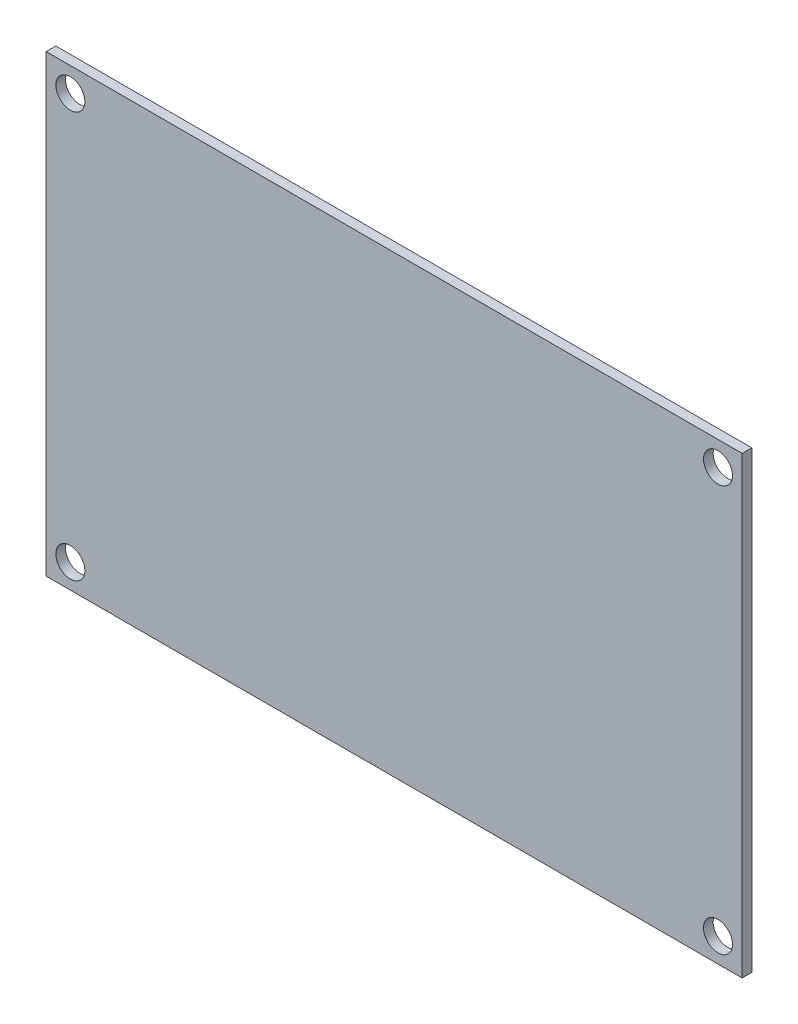
SolidWorks part; units mm, degrees
ref_plane "正面" through (0, 0, 0) normal (0, 0, 1) x (1, 0, 0)
ref_plane "平面" through (0, 0, 0) normal (0, 1, 0) x (1, 0, 0)
ref_plane "右側面" through (0, 0, 0) normal (1, 0, 0) x (0, 0, -1)
sketch "ｽｹｯﾁ1" plane through (0, 0, 0) normal (0, 0, 1) x (1, 0, 0)
  line L1 (-72, 47) -> (0, 47)
  line L2 (-72, 47) -> (-72, 0)
  line L3 (-72, 0) -> (0, 0)
  line L4 (0, 47) -> (0, 0)
  dimension "D1" = 47
  dimension "D2" = 72
extrude "ﾎﾞｽ - 押し出し1" add sketch "ｽｹｯﾁ1" along normal blind 1
sketch "ｽｹｯﾁ2" plane through (0, 0, 1) normal (0, 0, 1) x (1, 0, 0)
  line L0 (-72, 47) -> (-72, 0) construction
  line L1 (0, 47) -> (-72, 47) construction
  line L2 (-72, 0) -> (0, 0) construction
  line L3 (0, 0) -> (0, 47) construction
  circle A0 centre (-69.5, 44.5) radius 1.5
  circle A1 centre (-69.5, 2.5) radius 1.5
  circle A2 centre (-2.5, 44.5) radius 1.5
  circle A3 centre (-2.5, 2.5) radius 1.5
  dimension "D1" = 3
  dimension "D4" = 3
  dimension "D7" = 3
  dimension "D10" = 3
  dimension "D2" = 2.5
  dimension "D3" = 2.5
  dimension "D5" = 2.5
  dimension "D6" = 2.5
  dimension "D8" = 2.5
  dimension "D9" = 2.5
  dimension "D11" = 2.5
  dimension "D12" = 2.5
extrude "ｶｯﾄ - 押し出し1" cut sketch "ｽｹｯﾁ2" against normal through all
